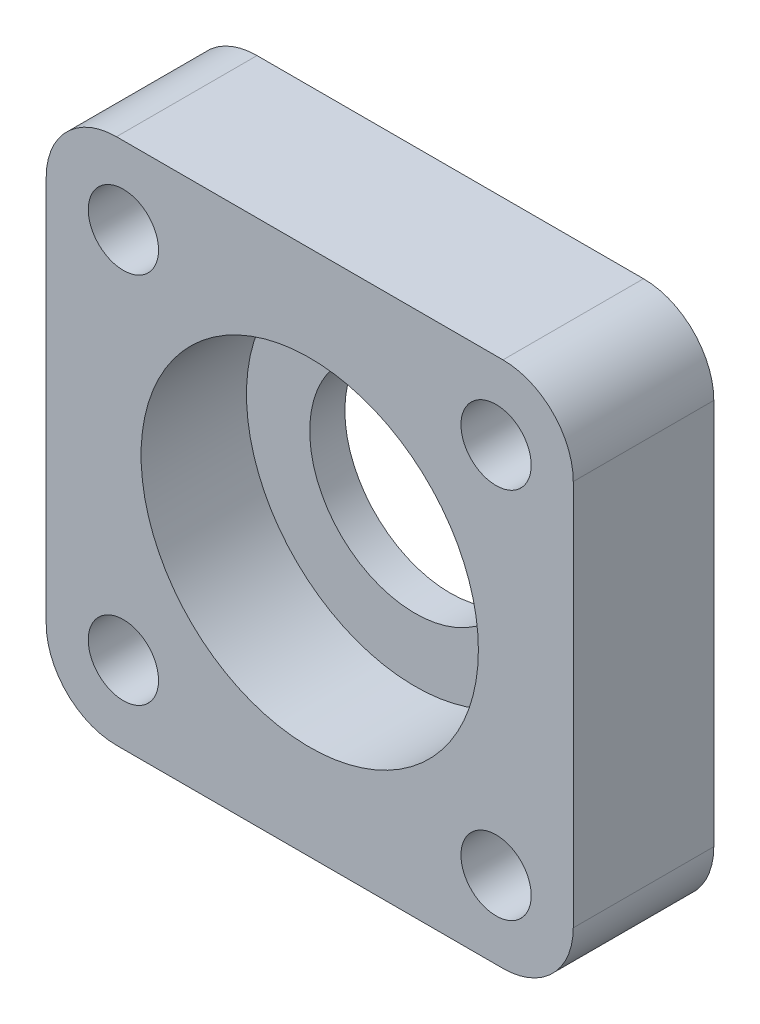
SolidWorks part; units mm, degrees
ref_plane "Front Plane" through (0, 0, 0) normal (0, 0, 1) x (1, 0, 0)
ref_plane "Top Plane" through (0, 0, 0) normal (0, 1, 0) x (1, 0, 0)
ref_plane "Right Plane" through (0, 0, 0) normal (1, 0, 0) x (0, 0, -1)
sketch "Sketch1" plane through (0, 0, 0) normal (0, 0, 1) x (1, 0, 0)
  line L0 (15, 15) -> (25.6066, 25.6066) construction
  line L1 (0, 0) -> (30, 0)
  line L2 (0, 0) -> (0, 30)
  line L3 (0, 30) -> (30, 30)
  line L4 (30, 0) -> (30, 30)
  line L5 (15, 15) -> (30, 15) construction
  circle A0 centre (15, 15) radius 15 construction
  circle A1 centre (25.6066, 25.6066) radius 2
  circle A2 centre (25.6066, 4.3934) radius 2
  circle A3 centre (4.3934, 4.3934) radius 2
  circle A4 centre (4.3934, 25.6066) radius 2
  point P19 (15, 15)
  dimension "D1" = 30
  dimension "D3" = 4
  dimension "D4" = 4
  dimension "D2" = 45
extrude "Boss-Extrude1" add sketch "Sketch1" along normal blind 8
sketch "Sketch2" plane through (0, 0, 8) normal (0, 0, 1) x (1, 0, 0)
  line L0 (30, 0) -> (30, 30) construction
  line L1 (30, 30) -> (0, 30) construction
  circle A0 centre (15, 15) radius 9.6
  dimension "D1" = 15
  dimension "D2" = 15
  dimension "D3" = 19.2
extrude "Cut-Extrude1" cut sketch "Sketch2" against normal blind 6
sketch "Sketch3" plane through (0, 0, 2) normal (0, 0, 1) x (1, 0, 0)
  circle A0 centre (15, 15) radius 6
  dimension "D1" = 12
extrude "Cut-Extrude2" cut sketch "Sketch3" against normal blind 7
fillet "Fillet1" radius 4 4 edges at (0, 0, 4) (30, 0, 4) (0, 30, 4) (30, 30, 4)
